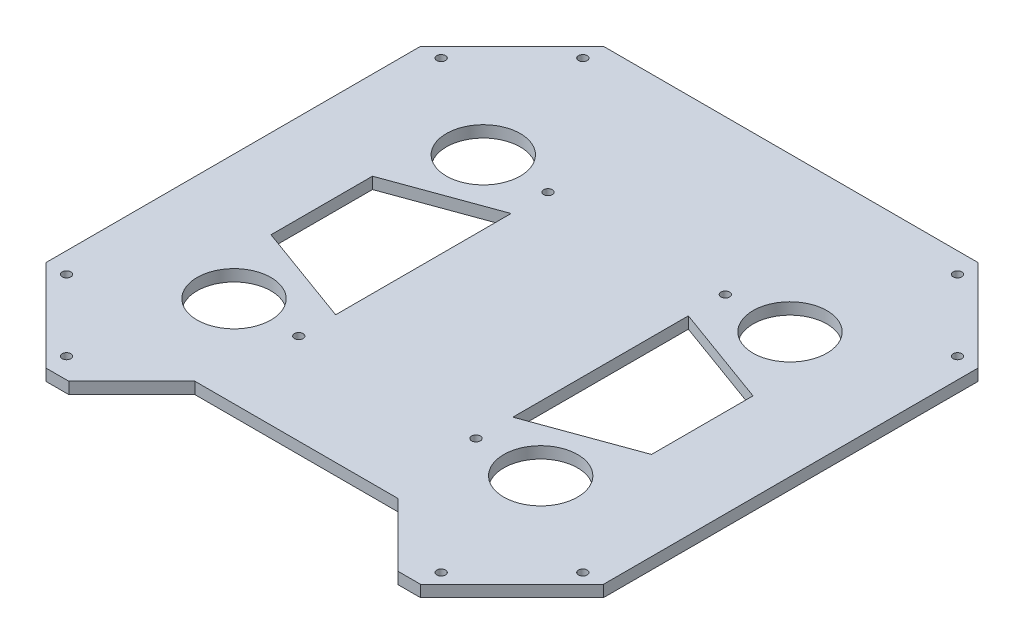
SolidWorks part; units mm, degrees
ref_plane "Front Plane" through (0, 0, 0) normal (0, 0, 1) x (1, 0, 0)
ref_plane "Top Plane" through (0, 0, 0) normal (0, 1, 0) x (1, 0, 0)
ref_plane "Right Plane" through (0, 0, 0) normal (1, 0, 0) x (0, 0, -1)
sketch "Sketch1" plane through (0, 0, 0) normal (0, 1, 0) x (1, 0, 0)
  line L0 (0, 0) -> (0, 724.3659) construction
  line L1 (0, 0) -> (205, 0)
  line L2 (305, 100) -> (305, 510)
  line L3 (205, 610) -> (-205, 610)
  line L4 (-305, 510) -> (-305, 100)
  line L6 (-305, 510) -> (-205, 610)
  line L7 (-205, 0) -> (205, 0)
  line L10 (0, 0) -> (205, 0)
  line L11 (305, 510) -> (205, 610)
  line L12 (305, 305) -> (-370.4931, 305) construction
  line L14 (-305, 100) -> (-205, 0)
  line L15 (305, 100) -> (205, 0)
  line L16 (-205, 610) -> (-305, 510)
  line L17 (-205, 610) -> (-136.4106, 541.4106)
  line L18 (-305, 510) -> (-236.4106, 441.4106)
  line L19 (-136.4106, 541.4106) -> (-236.4106, 441.4106)
  line L20 (305, 510) -> (205, 610)
  line L21 (305, 510) -> (236.4106, 441.4106)
  line L22 (136.4106, 541.4106) -> (236.4106, 441.4106)
  line L23 (205, 610) -> (136.4106, 541.4106)
  line L24 (305, 100) -> (236.4106, 168.5894)
  line L25 (305, 100) -> (205, 0)
  line L26 (136.4106, 68.5894) -> (236.4106, 168.5894)
  line L27 (205, 0) -> (136.4106, 68.5894)
  line L28 (-305, 100) -> (-205, 0)
  line L29 (-305, 100) -> (-236.4106, 168.5894)
  line L30 (-205, 0) -> (-136.4106, 68.5894)
  line L31 (-136.4106, 68.5894) -> (-236.4106, 168.5894)
  line L32 (205, 610) -> (136.4106, 541.4106)
  line L33 (205, 610) -> (305, 510)
  line L34 (136.4106, 541.4106) -> (236.4106, 441.4106)
  line L35 (305, 510) -> (236.4106, 441.4106)
  line L36 (-305, 100) -> (-205, 0)
  line L37 (-305, 100) -> (-236.4106, 168.5894)
  line L38 (-205, 0) -> (-136.4106, 68.5894)
  line L39 (-236.4106, 168.5894) -> (-136.4106, 68.5894)
  line L40 (236.4106, 168.5894) -> (136.4106, 68.5894)
  line L41 (236.4106, 168.5894) -> (305, 100)
  line L42 (136.4106, 68.5894) -> (205, 0)
  line L43 (305, 100) -> (205, 0)
  line L45 (0, 610) -> (-84.25, 610)
  line L46 (0, 0) -> (-84.25, 0)
  line L47 (-84.25, 610) -> (-84.25, 0)
  line L48 (84.25, 610) -> (84.25, 0)
  line L49 (-84.25, 610) -> (84.25, 610)
  line L50 (-84.25, 610) -> (-84.25, 0)
  line L51 (84.25, 610) -> (84.25, 0)
  line L52 (-84.25, 0) -> (84.25, 0)
  line L53 (-167.8213, 441.4106) -> (-97, 441.4106)
  line L54 (-84.25, 76.4) -> (84.25, 76.4)
  line L55 (-84.25, 76.4) -> (-84.25, 533.6)
  line L56 (84.25, 76.4) -> (84.25, 533.6)
  line L57 (-84.25, 533.6) -> (84.25, 533.6)
  line L70 (-305, 510) -> (-236.4106, 441.4106)
  circle A0 centre (-167.8213, 441.4106) radius 40.4
  circle A1 centre (-167.8213, 168.5894) radius 40.4
  circle A2 centre (167.8213, 168.5894) radius 40.4
  circle A3 centre (167.8213, 441.4106) radius 40.4
  arc A4 (-84.25, 76.4) -> (84.25, 76.4) centre (0, 76.4) ccw
  circle A9 centre (-97, 441.4106) radius 4.7625
  circle A10 centre (97, 441.4106) radius 4.7625
  circle A11 centre (97, 168.5894) radius 4.7625
  circle A12 centre (-97, 168.5894) radius 4.7625
  point P47 (-270.7053, 475.7053)
  dimension "D6" = 80.8
  dimension "D10" = 48.5
  dimension "D15" = 9.525
  dimension "D16" = 48.5
  dimension "D1" = 610
  dimension "D2" = 610
  dimension "D3" = 97
  dimension "D4" = 45
  dimension "D5" = 100
  dimension "D7" = 168.5
  dimension "D8" = 84.25
  dimension "D9" = 84.25
  dimension "D11" = 457.2
  dimension "D13" = 533.6
  dimension "D14" = 194
extrude "Boss-Extrude1" add sketch "Sketch1" along normal blind 12.7 contours L19 L17 L6 L18 | L39 A1 L31 L30 L7 L47 L3 L17 L19 A0 L18 L4 L29 | L30 L31 L39 L29 L14 | L48 L3 L47 L7 L1 | L34 A3 L22 L23 L3 L48 L10 L27 L26 A2 L40 L24 L2 L21 | L11 L23 L22 L34 L21 | L27 L15 L24 L40 L26 | L54 L55 L57 L56 | L49 L50 L52 L51
sketch "Sketch2" plane through (0, 12.7, 0) normal (0, 1, 0) x (1, 0, 0)
  line L4 (-205, 0) -> (-180, 0)
  line L5 (-180, 0) -> (-111, 69)
  line L6 (-180, 0) -> (180, 0)
  line L7 (180, 0) -> (111, 69)
  line L8 (111, 69) -> (-111, 69)
  line L10 (180, 0) -> (205, 0)
  line M5 (-205, 0) -> (205, 0)
  dimension "D1" = 25
  dimension "D2" = 25
  dimension "D3" = 45
  dimension "D4" = 69
  dimension "D5" = 45
extrude "Cut-Extrude1" cut sketch "Sketch2" against normal blind 5000 contours L7 L8 L5 M5
sketch "Sketch3" plane through (0, 12.7, 0) normal (0, 1, 0) x (1, 0, 0)
  line L0 (0, 0) -> (0, 610) construction
  line L1 (-305, 305) -> (305, 305) construction
  line L2 (-305, 100) -> (-205, 0) construction
  line L4 (-282.5423, 100) -> (-293.7711, 88.7711)
  line L5 (205, 610) -> (-205, 610) construction
  line L6 (-305, 510) -> (-305, 100) construction
  line L7 (305, 100) -> (305, 510) construction
  line L8 (-180, 0) -> (-111, 69) construction
  circle A0 centre (-205, 22.4577) radius 4.7625
  circle A1 centre (205, 22.4577) radius 4.7625
  circle A2 centre (-282.5423, 100) radius 4.7625
  circle A3 centre (282.5423, 100) radius 4.7625
  circle A4 centre (282.5423, 510) radius 4.7625
  circle A5 centre (205, 587.5423) radius 4.7625
  circle A6 centre (-205, 587.5423) radius 4.7625
  circle A7 centre (-282.5423, 510) radius 4.7625
  dimension "D1" = 9.525
  dimension "D2" = 9.525
  dimension "D6" = 15.88
  dimension "D5" = 33.5577
  dimension "D3" = 15.88
  dimension "D4" = 15.88
  dimension "D7" = 15.88
extrude "Cut-Extrude2" cut sketch "Sketch3" against normal blind 5000 contours A2 | A0 | A1 | A3 | A4 | A5 | A6 | A7
sketch "Sketch4" plane through (0, 12.7, 0) normal (0, 1, 0) x (1, 0, 0)
  line L0 (0, 610) -> (0, 69)
  line L1 (0, 610) -> (69.7563, 610)
  line L2 (0, 69) -> (69.7563, 69)
  line L3 (69.7563, 610) -> (69.7563, 69)
  line L4 (205, 610) -> (-205, 610) construction
  line L5 (111, 69) -> (-111, 69) construction
  line L6 (0, 69) -> (0, 610)
  line L7 (0, 69) -> (-74.0097, 69)
  line L8 (0, 610) -> (-74.0097, 610)
  line L9 (-74.0097, 69) -> (-74.0097, 610)
  line L10 (0, 0) -> (0, 637.1931) construction
  line L19 (-97, 401.0106) -> (-97, 208.9894)
  line L20 (-97, 208.9894) -> (-208.2213, 249.4706)
  line L21 (-208.2213, 249.4706) -> (-208.2213, 360.5294)
  line L22 (-97, 441.4106) -> (-97, 168.5894)
  line L23 (-208.2213, 441.4106) -> (-208.2213, 168.5894)
  line L24 (-208.2213, 360.5294) -> (-97, 401.0106)
  line L25 (-208.2213, 441.4106) -> (-167.8213, 441.4106)
  line L26 (-167.8213, 401.0106) -> (-97, 401.0106)
  line L27 (-167.8213, 208.9894) -> (-97, 208.9894)
  line L28 (208.2213, 249.4706) -> (208.2213, 360.5294)
  line L29 (97, 208.9894) -> (208.2213, 249.4706)
  line L30 (97, 401.0106) -> (97, 208.9894)
  line L31 (208.2213, 360.5294) -> (97, 401.0106)
  circle A0 centre (-167.8213, 441.4106) radius 40.4 construction
  circle A1 centre (-167.8213, 168.5894) radius 40.4 construction
  dimension "D1" = 70.8213
  dimension "D2" = 70.8213
  dimension "D3" = 20
  dimension "D4" = 20
extrude "Cut-Extrude3" cut sketch "Sketch4" against normal blind 20 contours L24 L21 L20 L19 | L28 L31 L30 L29
